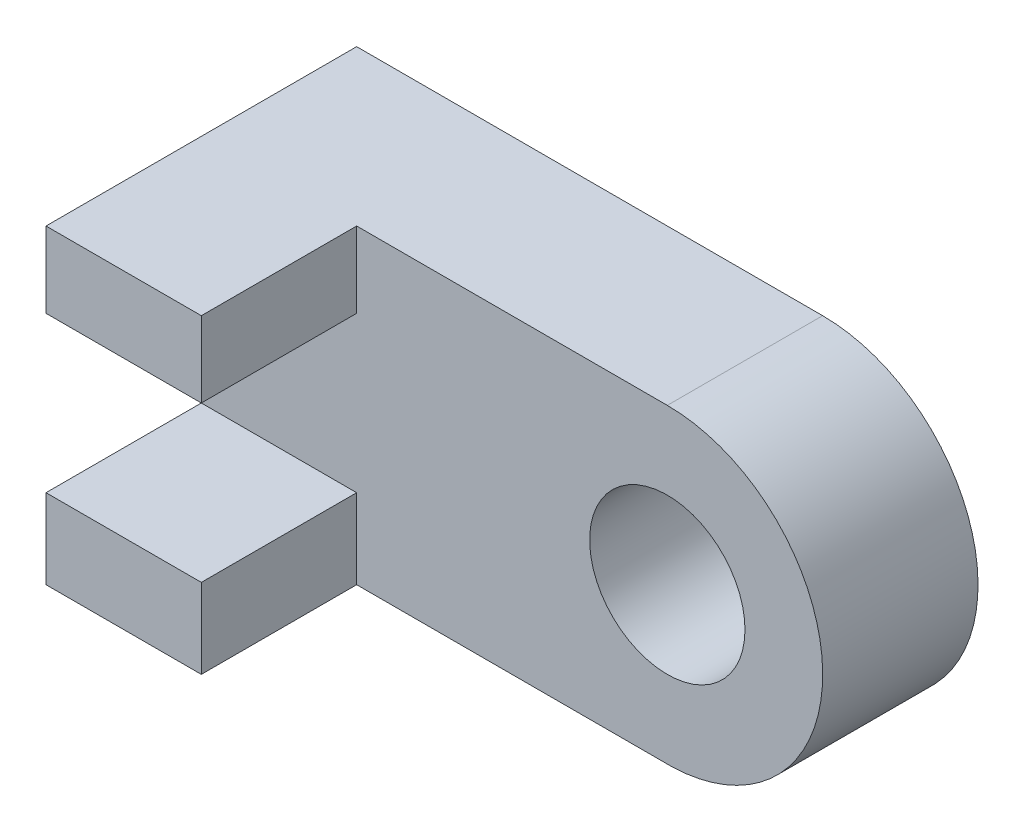
SolidWorks part; units mm, degrees
material "Cedar"
ref_plane "Frontal" through (0, 0, 0) normal (0, 0, 1) x (1, 0, 0)
ref_plane "Horizontal" through (0, 0, 0) normal (0, 1, 0) x (1, 0, 0)
ref_plane "Profile" through (0, 0, 0) normal (1, 0, 0) x (0, 0, -1)
sketch "Sketch2" plane through (0, 0, 0) normal (0, 0, 1) x (1, 0, 0)
  line L0 (-68.5102, 50.1293) -> (33.0898, 50.1293)
  line L1 (-68.5102, -51.4707) -> (34.8104, -51.4707)
  line L2 (-68.5102, -51.4707) -> (-68.5102, 50.1293)
  line L3 (-88.8921, -0.6707) -> (90.6543, -0.6707) construction
  arc A0 (33.0898, 50.1293) -> (34.8104, -51.4707) centre (33.0898, -0.6853) cw
  dimension "D1" = 101.6
  dimension "D2" = 101.6
extrude "Extrude1" add sketch "Sketch2" along normal blind 50.8
sketch "Sketch3" plane through (-68.5102, 0, 0) normal (-1, 0, 0) x (0, 0, 1)
  line L0 (50.8, 50.1293) -> (101.6, 50.1293)
  line L1 (101.6, 50.1293) -> (101.6, -51.4707)
  line L2 (101.6, -51.4707) -> (50.8, -51.4707)
  line L3 (-17.1256, 0) -> (101.6, 0) construction
  line L8 (0, 50.1293) -> (0, -51.4707)
  line L9 (0, -51.4707) -> (50.8, -51.4707)
  line L10 (50.8, -51.4707) -> (50.8, 50.1293)
  line L11 (50.8, 50.1293) -> (0, 50.1293)
  line L12 (0, 50.1293) -> (0, -51.4707)
  line L13 (0, -51.4707) -> (50.8, -51.4707)
  line L15 (50.8, 50.1293) -> (0, 50.1293)
  dimension "D1" = 50.8
  dimension "D2" = 0
extrude "Extrude2" add sketch "Sketch3" along normal blind 50.8
ref_plane "Plane1" through (-68.5102, 50.1293, 101.6) normal (0, 1, 0) x (-1, 0, 0)
sketch "Sketch5" plane through (-68.5102, 0, 0) normal (1, 0, 0) x (0, 0, -1)
  line L1 (-101.6, 25.3949) -> (-50.8, 25.3949)
  line L2 (-101.6, -51.4707) -> (-101.6, 50.1293) construction
  line L3 (-50.8, 50.1293) -> (-50.8, -51.4707) construction
  line L4 (-50.8, 25.3949) -> (-50.8, -25.4051)
  line L6 (4.3704, 0) -> (-117.2762, 0) construction
  line L7 (-50.8, -25.4051) -> (-101.6, -25.4051)
  line L8 (-101.6, -25.4051) -> (-101.6, 25.3949)
extrude "Cut-Extrude1" cut sketch "Sketch5" against normal blind 50.8
sketch "Sketch6" plane through (0, 0, 50.8) normal (0, 0, 1) x (1, 0, 0)
  circle A1 centre (33.0898, -0.6853) radius 25.4
extrude "Cut-Extrude2" cut sketch "Sketch6" against normal through all
